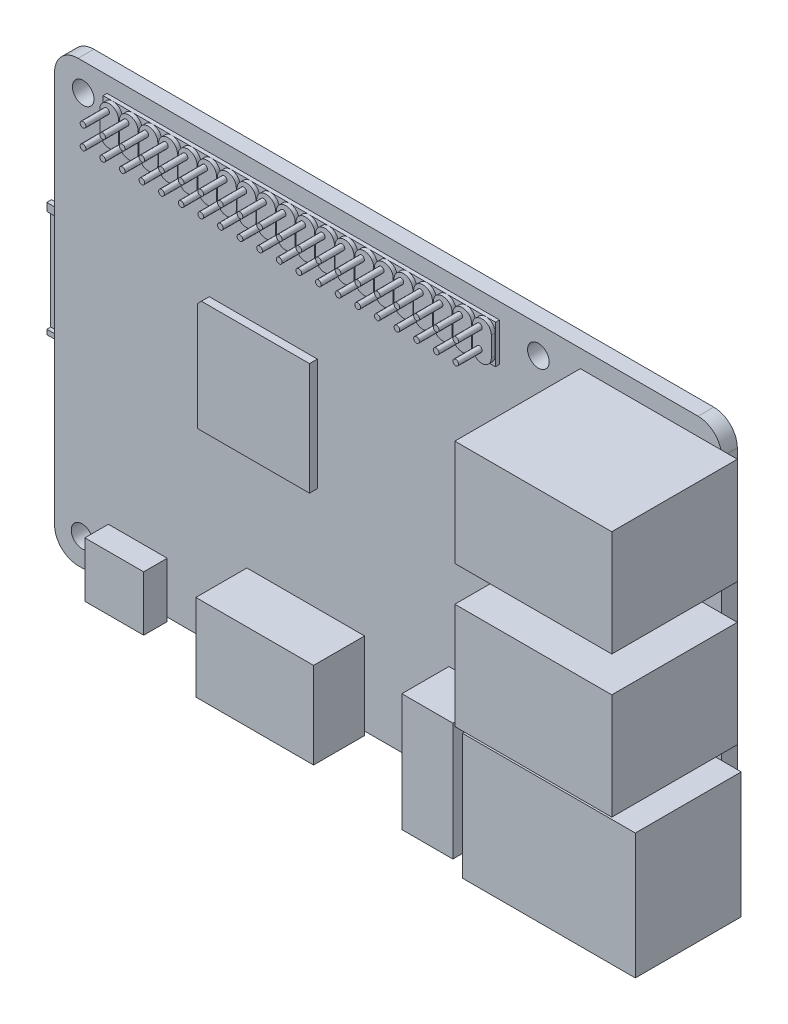
SolidWorks part; units mm, degrees
ref_plane "Plan de face" through (0, 0, 0) normal (0, 0, 1) x (1, 0, 0)
ref_plane "Plan de dessus" through (0, 0, 0) normal (0, 1, 0) x (1, 0, 0)
ref_plane "Plan de droite" through (0, 0, 0) normal (1, 0, 0) x (0, 0, -1)
sketch "Esquisse13" plane through (0, 0, 0) normal (0, 0, 1) x (1, 0, 0)
  line L1 (32.3051, 232.7529) -> (111.3051, 232.7529)
  line L2 (29.3051, 229.7529) -> (29.3051, 179.7529)
  line L3 (32.3051, 176.7529) -> (111.3051, 176.7529)
  line L4 (114.3051, 229.7529) -> (114.3051, 179.7529)
  arc A0 (114.3051, 229.7529) -> (111.3051, 232.7529) centre (111.3051, 229.7529) ccw
  arc A1 (114.3051, 179.7529) -> (111.3051, 176.7529) centre (111.3051, 179.7529) cw
  arc A2 (32.3051, 176.7529) -> (29.3051, 179.7529) centre (32.3051, 179.7529) cw
  arc A3 (32.3051, 232.7529) -> (29.3051, 229.7529) centre (32.3051, 229.7529) ccw
  dimension "D1" = 3
  dimension "D2" = 56
  dimension "D3" = 85
extrude "Boss.-Extru.6" add sketch "Esquisse13" along normal blind 2 separate body
sketch "Esquisse18" plane through (0, 0, 2) normal (0, 0, 1) x (1, 0, 0)
  line L0 (37.2566, 229.5258) -> (37.2566, 226.9968) construction
  line L1 (38.4539, 229.5258) -> (38.4539, 226.9968)
  line L2 (36.0594, 229.5258) -> (36.0594, 226.9968)
  line L3 (39.7566, 229.5258) -> (39.7566, 226.9968) construction
  line L4 (40.9539, 229.5258) -> (40.9539, 226.9968)
  line L5 (38.5594, 229.5258) -> (38.5594, 226.9968)
  line L6 (42.2566, 229.5258) -> (42.2566, 226.9968) construction
  line L7 (43.4539, 229.5258) -> (43.4539, 226.9968)
  line L8 (41.0594, 229.5258) -> (41.0594, 226.9968)
  line L9 (44.7566, 229.5258) -> (44.7566, 226.9968) construction
  line L10 (45.9539, 229.5258) -> (45.9539, 226.9968)
  line L11 (43.5594, 229.5258) -> (43.5594, 226.9968)
  line L12 (47.2566, 229.5258) -> (47.2566, 226.9968) construction
  line L13 (48.4539, 229.5258) -> (48.4539, 226.9968)
  line L14 (46.0594, 229.5258) -> (46.0594, 226.9968)
  line L15 (49.7566, 229.5258) -> (49.7566, 226.9968) construction
  line L16 (50.9539, 229.5258) -> (50.9539, 226.9968)
  line L17 (48.5594, 229.5258) -> (48.5594, 226.9968)
  line L18 (52.2566, 229.5258) -> (52.2566, 226.9968) construction
  line L19 (53.4539, 229.5258) -> (53.4539, 226.9968)
  line L20 (51.0594, 229.5258) -> (51.0594, 226.9968)
  line L21 (54.7566, 229.5258) -> (54.7566, 226.9968) construction
  line L22 (55.9539, 229.5258) -> (55.9539, 226.9968)
  line L23 (53.5594, 229.5258) -> (53.5594, 226.9968)
  line L24 (57.2566, 229.5258) -> (57.2566, 226.9968) construction
  line L25 (58.4539, 229.5258) -> (58.4539, 226.9968)
  line L26 (56.0594, 229.5258) -> (56.0594, 226.9968)
  line L27 (59.7566, 229.5258) -> (59.7566, 226.9968) construction
  line L28 (60.9539, 229.5258) -> (60.9539, 226.9968)
  line L29 (58.5594, 229.5258) -> (58.5594, 226.9968)
  line L30 (62.2566, 229.5258) -> (62.2566, 226.9968) construction
  line L31 (63.4539, 229.5258) -> (63.4539, 226.9968)
  line L32 (61.0594, 229.5258) -> (61.0594, 226.9968)
  line L33 (64.7566, 229.5258) -> (64.7566, 226.9968) construction
  line L34 (65.9539, 229.5258) -> (65.9539, 226.9968)
  line L35 (63.5594, 229.5258) -> (63.5594, 226.9968)
  line L36 (67.2566, 229.5258) -> (67.2566, 226.9968) construction
  line L37 (68.4539, 229.5258) -> (68.4539, 226.9968)
  line L38 (66.0594, 229.5258) -> (66.0594, 226.9968)
  line L39 (69.7566, 229.5258) -> (69.7566, 226.9968) construction
  line L40 (70.9539, 229.5258) -> (70.9539, 226.9968)
  line L41 (68.5594, 229.5258) -> (68.5594, 226.9968)
  line L42 (72.2566, 229.5258) -> (72.2566, 226.9968) construction
  line L43 (73.4539, 229.5258) -> (73.4539, 226.9968)
  line L44 (71.0594, 229.5258) -> (71.0594, 226.9968)
  line L45 (74.7566, 229.5258) -> (74.7566, 226.9968) construction
  line L46 (75.9539, 229.5258) -> (75.9539, 226.9968)
  line L47 (73.5594, 229.5258) -> (73.5594, 226.9968)
  line L48 (77.2566, 229.5258) -> (77.2566, 226.9968) construction
  line L49 (78.4539, 229.5258) -> (78.4539, 226.9968)
  line L50 (76.0594, 229.5258) -> (76.0594, 226.9968)
  line L51 (79.7566, 229.5258) -> (79.7566, 226.9968) construction
  line L52 (80.9539, 229.5258) -> (80.9539, 226.9968)
  line L53 (78.5594, 229.5258) -> (78.5594, 226.9968)
  line L54 (82.2566, 229.5258) -> (82.2566, 226.9968) construction
  line L55 (83.4539, 229.5258) -> (83.4539, 226.9968)
  line L56 (81.0594, 229.5258) -> (81.0594, 226.9968)
  line L57 (84.7566, 229.5258) -> (84.7566, 226.9968) construction
  line L58 (85.9539, 229.5258) -> (85.9539, 226.9968)
  line L59 (83.5594, 229.5258) -> (83.5594, 226.9968)
  arc A0 (38.4539, 229.5258) -> (36.0594, 229.5258) centre (37.2566, 229.5258) ccw
  arc A1 (36.0594, 226.9968) -> (38.4539, 226.9968) centre (37.2566, 226.9968) ccw
  arc A2 (40.9539, 229.5258) -> (38.5594, 229.5258) centre (39.7566, 229.5258) ccw
  arc A3 (38.5594, 226.9968) -> (40.9539, 226.9968) centre (39.7566, 226.9968) ccw
  arc A4 (43.4539, 229.5258) -> (41.0594, 229.5258) centre (42.2566, 229.5258) ccw
  arc A5 (41.0594, 226.9968) -> (43.4539, 226.9968) centre (42.2566, 226.9968) ccw
  arc A6 (45.9539, 229.5258) -> (43.5594, 229.5258) centre (44.7566, 229.5258) ccw
  arc A7 (43.5594, 226.9968) -> (45.9539, 226.9968) centre (44.7566, 226.9968) ccw
  arc A8 (48.4539, 229.5258) -> (46.0594, 229.5258) centre (47.2566, 229.5258) ccw
  arc A9 (46.0594, 226.9968) -> (48.4539, 226.9968) centre (47.2566, 226.9968) ccw
  arc A10 (50.9539, 229.5258) -> (48.5594, 229.5258) centre (49.7566, 229.5258) ccw
  arc A11 (48.5594, 226.9968) -> (50.9539, 226.9968) centre (49.7566, 226.9968) ccw
  arc A12 (53.4539, 229.5258) -> (51.0594, 229.5258) centre (52.2566, 229.5258) ccw
  arc A13 (51.0594, 226.9968) -> (53.4539, 226.9968) centre (52.2566, 226.9968) ccw
  arc A14 (55.9539, 229.5258) -> (53.5594, 229.5258) centre (54.7566, 229.5258) ccw
  arc A15 (53.5594, 226.9968) -> (55.9539, 226.9968) centre (54.7566, 226.9968) ccw
  arc A16 (58.4539, 229.5258) -> (56.0594, 229.5258) centre (57.2566, 229.5258) ccw
  arc A17 (56.0594, 226.9968) -> (58.4539, 226.9968) centre (57.2566, 226.9968) ccw
  arc A18 (60.9539, 229.5258) -> (58.5594, 229.5258) centre (59.7566, 229.5258) ccw
  arc A19 (58.5594, 226.9968) -> (60.9539, 226.9968) centre (59.7566, 226.9968) ccw
  arc A20 (63.4539, 229.5258) -> (61.0594, 229.5258) centre (62.2566, 229.5258) ccw
  arc A21 (61.0594, 226.9968) -> (63.4539, 226.9968) centre (62.2566, 226.9968) ccw
  arc A22 (65.9539, 229.5258) -> (63.5594, 229.5258) centre (64.7566, 229.5258) ccw
  arc A23 (63.5594, 226.9968) -> (65.9539, 226.9968) centre (64.7566, 226.9968) ccw
  arc A24 (68.4539, 229.5258) -> (66.0594, 229.5258) centre (67.2566, 229.5258) ccw
  arc A25 (66.0594, 226.9968) -> (68.4539, 226.9968) centre (67.2566, 226.9968) ccw
  arc A26 (70.9539, 229.5258) -> (68.5594, 229.5258) centre (69.7566, 229.5258) ccw
  arc A27 (68.5594, 226.9968) -> (70.9539, 226.9968) centre (69.7566, 226.9968) ccw
  arc A28 (73.4539, 229.5258) -> (71.0594, 229.5258) centre (72.2566, 229.5258) ccw
  arc A29 (71.0594, 226.9968) -> (73.4539, 226.9968) centre (72.2566, 226.9968) ccw
  arc A30 (75.9539, 229.5258) -> (73.5594, 229.5258) centre (74.7566, 229.5258) ccw
  arc A31 (73.5594, 226.9968) -> (75.9539, 226.9968) centre (74.7566, 226.9968) ccw
  arc A32 (78.4539, 229.5258) -> (76.0594, 229.5258) centre (77.2566, 229.5258) ccw
  arc A33 (76.0594, 226.9968) -> (78.4539, 226.9968) centre (77.2566, 226.9968) ccw
  arc A34 (80.9539, 229.5258) -> (78.5594, 229.5258) centre (79.7566, 229.5258) ccw
  arc A35 (78.5594, 226.9968) -> (80.9539, 226.9968) centre (79.7566, 226.9968) ccw
  arc A36 (83.4539, 229.5258) -> (81.0594, 229.5258) centre (82.2566, 229.5258) ccw
  arc A37 (81.0594, 226.9968) -> (83.4539, 226.9968) centre (82.2566, 226.9968) ccw
  arc A38 (85.9539, 229.5258) -> (83.5594, 229.5258) centre (84.7566, 229.5258) ccw
  arc A39 (83.5594, 226.9968) -> (85.9539, 226.9968) centre (84.7566, 226.9968) ccw
  point P2 (37.2566, 228.2613)
  point P11 (39.7566, 228.2613)
  point P18 (42.2566, 228.2613)
  point P25 (44.7566, 228.2613)
  point P32 (47.2566, 228.2613)
  point P39 (49.7566, 228.2613)
  point P46 (52.2566, 228.2613)
  point P53 (54.7566, 228.2613)
  point P60 (57.2566, 228.2613)
  point P67 (59.7566, 228.2613)
  point P74 (62.2566, 228.2613)
  point P81 (64.7566, 228.2613)
  point P88 (67.2566, 228.2613)
  point P95 (69.7566, 228.2613)
  point P102 (72.2566, 228.2613)
  point P109 (74.7566, 228.2613)
  point P116 (77.2566, 228.2613)
  point P123 (79.7566, 228.2613)
  point P130 (82.2566, 228.2613)
  point P137 (84.7566, 228.2613)
  dimension "D1" = 20
extrude "Boss.-Extru.8" add sketch "Esquisse18" along normal blind 1
sketch "Esquisse19" plane through (0, 0, 2) normal (0, 0, 1) x (1, 0, 0)
  line L1 (35.9943, 230.7231) -> (85.9948, 230.7231)
  line L2 (35.9943, 230.7231) -> (35.9943, 225.7996)
  line L3 (35.9943, 225.7996) -> (85.9948, 225.7996)
  line L4 (85.9948, 230.7231) -> (85.9948, 225.7996)
  arc A0 (36.0594, 226.9968) -> (38.4539, 226.9968) centre (37.2566, 226.9968) ccw construction
  arc A1 (38.4539, 229.5258) -> (36.0594, 229.5258) centre (37.2566, 229.5258) ccw construction
extrude "Boss.-Extru.9" add sketch "Esquisse19" along normal blind 0.5
sketch "Esquisse20" plane through (0, 0, 3) normal (0, 0, 1) x (1, 0, 0)
  line L0 (36.9236, 229.735) -> (36.9236, 227.2302) construction
  circle A0 centre (36.9236, 229.735) radius 0.3614
  circle A1 centre (36.9236, 227.2302) radius 0.3614
  circle A2 centre (39.4236, 229.735) radius 0.3614
  circle A3 centre (39.4236, 227.2302) radius 0.3614
  circle A4 centre (41.9236, 229.735) radius 0.3614
  circle A5 centre (41.9236, 227.2302) radius 0.3614
  circle A6 centre (44.4236, 229.735) radius 0.3614
  circle A7 centre (44.4236, 227.2302) radius 0.3614
  circle A8 centre (46.9236, 229.735) radius 0.3614
  circle A9 centre (46.9236, 227.2302) radius 0.3614
  circle A10 centre (49.4236, 229.735) radius 0.3614
  circle A11 centre (49.4236, 227.2302) radius 0.3614
  circle A12 centre (51.9236, 229.735) radius 0.3614
  circle A13 centre (51.9236, 227.2302) radius 0.3614
  circle A14 centre (54.4236, 229.735) radius 0.3614
  circle A15 centre (54.4236, 227.2302) radius 0.3614
  circle A16 centre (56.9236, 229.735) radius 0.3614
  circle A17 centre (56.9236, 227.2302) radius 0.3614
  circle A18 centre (59.4236, 229.735) radius 0.3614
  circle A19 centre (59.4236, 227.2302) radius 0.3614
  circle A20 centre (61.9236, 229.735) radius 0.3614
  circle A21 centre (61.9236, 227.2302) radius 0.3614
  circle A22 centre (64.4236, 229.735) radius 0.3614
  circle A23 centre (64.4236, 227.2302) radius 0.3614
  circle A24 centre (66.9236, 229.735) radius 0.3614
  circle A25 centre (66.9236, 227.2302) radius 0.3614
  circle A26 centre (69.4236, 229.735) radius 0.3614
  circle A27 centre (69.4236, 227.2302) radius 0.3614
  circle A28 centre (71.9236, 229.735) radius 0.3614
  circle A29 centre (71.9236, 227.2302) radius 0.3614
  circle A30 centre (74.4236, 229.735) radius 0.3614
  circle A31 centre (74.4236, 227.2302) radius 0.3614
  circle A32 centre (76.9236, 229.735) radius 0.3614
  circle A33 centre (76.9236, 227.2302) radius 0.3614
  circle A34 centre (79.4236, 229.735) radius 0.3614
  circle A35 centre (79.4236, 227.2302) radius 0.3614
  circle A36 centre (81.9236, 229.735) radius 0.3614
  circle A37 centre (81.9236, 227.2302) radius 0.3614
  circle A38 centre (84.4236, 229.735) radius 0.3614
  circle A39 centre (84.4236, 227.2302) radius 0.3614
  dimension "D1" = 20
extrude "Boss.-Extru.10" add sketch "Esquisse20" along normal blind 3
sketch "Esquisse21" plane through (0, 0, 2) normal (0, 0, 1) x (1, 0, 0)
  line L0 (48.4885, 214.2688) -> (49.0165, 214.7968)
  line L1 (62.7885, 200.4968) -> (48.4885, 200.4968)
  line L2 (62.7885, 200.4968) -> (62.7885, 214.7968)
  line L3 (62.7885, 214.7968) -> (49.0165, 214.7968)
  line L4 (48.4885, 200.4968) -> (48.4885, 214.2688)
  line L5 (91.8038, 213.7838) -> (92.0748, 213.5724)
  line L6 (83.9048, 205.5938) -> (92.0748, 205.5938)
  line L7 (83.9048, 205.5938) -> (83.9048, 213.7838)
  line L8 (83.9048, 213.7838) -> (91.8038, 213.7838)
  line L9 (92.0748, 205.5938) -> (92.0748, 213.5724)
  dimension "D1" = 14.3
  dimension "D2" = 14.3
  dimension "D3" = 8.17
  dimension "D4" = 8.19
extrude "Boss.-Extru.11" add sketch "Esquisse21" along normal blind 1
sketch "Esquisse22" plane through (0, 0, 0) normal (0, 0, -1) x (-1, 0, 0)
  line L0 (-77.9075, 215.1199) -> (-77.5535, 215.4739)
  line L1 (-65.8326, 203.3272) -> (-77.9075, 203.3272)
  line L2 (-65.8326, 203.3272) -> (-65.8326, 215.4739)
  line L3 (-65.8326, 215.4739) -> (-77.5535, 215.4739)
  line L4 (-77.9075, 203.3272) -> (-77.9075, 215.1199)
extrude "Boss.-Extru.12" add sketch "Esquisse22" along normal blind 1
sketch "Esquisse23" plane through (0, 0, 2) normal (0, 0, 1) x (1, 0, 0)
  line L0 (32.3051, 176.7529) -> (111.3051, 176.7529) construction
  line L1 (29.3051, 229.7529) -> (29.3051, 179.7529) construction
  circle A0 centre (32.9513, 229.2529) radius 1.375
  circle A1 centre (32.8051, 180.2529) radius 1.375
  circle A2 centre (90.8051, 180.2529) radius 1.375
  circle A3 centre (90.9513, 229.2529) radius 1.375
  point P12 (0, 0)
  point P13 (0, 0)
  point P14 (0, 0)
  dimension "D7" = 2.75
  dimension "D1" = 58
  dimension "D2" = 58
  dimension "D3" = 49
  dimension "D4" = 49
  dimension "D5" = 3.5
  dimension "D6" = 3.5
extrude "Enlèv. mat.-Extru.1" cut sketch "Esquisse23" against normal blind 21
sketch "Esquisse24" plane through (0, 0, 0) normal (0, 0, -1) x (-1, 0, 0)
  line L0 (-111.3051, 232.7529) -> (-32.3051, 232.7529) construction
  line L1 (-43.9051, 212.8529) -> (-26.3051, 212.8529)
  line L2 (-43.9051, 212.8529) -> (-43.9051, 198.2529)
  line L3 (-43.9051, 198.2529) -> (-26.3051, 198.2529)
  line L4 (-26.3051, 212.8529) -> (-26.3051, 198.2529)
  line L5 (-29.3051, 229.7529) -> (-29.3051, 179.7529) construction
  dimension "D1" = 19.9
  dimension "D2" = 17.6
  dimension "D3" = 3
  dimension "D4" = 14.6
extrude "Boss.-Extru.13" add sketch "Esquisse24" along normal blind 0.6
sketch "Esquisse25" plane through (26.3051, 0, 0) normal (-1, 0, 0) x (0, 0, 1)
  line L0 (-0.6, 212.8529) -> (0, 212.8529) construction
  line L1 (-0.5, 211.8529) -> (0, 211.8529)
  line L2 (-0.5, 211.8529) -> (-0.5, 198.8529)
  line L3 (-0.5, 198.8529) -> (0, 198.8529)
  line L4 (0, 211.8529) -> (0, 198.8529)
  line L5 (0, 229.7529) -> (0, 212.8529) construction
  line L6 (0, 198.2529) -> (0, 212.8529) construction
  line L7 (0, 203.3272) -> (0, 215.4739) construction
  dimension "D1" = 0.5
  dimension "D2" = 13
  dimension "D3" = 1
extrude "Enlèv. mat.-Extru.2" cut sketch "Esquisse25" against normal blind 11
sketch "Sketch1" plane through (0, 0, 2) normal (0, 0, 1) x (1, 0, 0)
  line L0 (32.3051, 176.7529) -> (111.3051, 176.7529) construction
  line L1 (36.1551, 176.2529) -> (43.6551, 176.2529)
  line L2 (36.1551, 176.2529) -> (36.1551, 183.2529)
  line L3 (36.1551, 183.2529) -> (43.6551, 183.2529)
  line L4 (43.6551, 176.2529) -> (43.6551, 183.2529)
  line L5 (39.9051, 183.2529) -> (39.9051, 176.2529) construction
  line L6 (29.3051, 229.7529) -> (29.3051, 179.7529) construction
  dimension "D1" = 7.5
  dimension "D2" = 7
  dimension "D3" = 0.5
  dimension "D4" = 10.6
extrude "Boss-Extrude1" add sketch "Sketch1" along normal blind 3
sketch "Sketch2" plane through (0, 0, 2) normal (0, 0, 1) x (1, 0, 0)
  line L0 (114.3051, 179.7529) -> (114.3051, 229.7529) construction
  line L1 (94.8051, 180.2529) -> (116.8051, 180.2529)
  line L2 (94.8051, 180.2529) -> (94.8051, 196.2529)
  line L3 (94.8051, 196.2529) -> (116.8051, 196.2529)
  line L4 (116.8051, 180.2529) -> (116.8051, 196.2529)
  line L5 (94.8051, 188.2529) -> (116.8051, 188.2529) construction
  line L6 (43.6551, 176.7529) -> (111.3051, 176.7529) construction
  dimension "D1" = 16
  dimension "D2" = 2.5
  dimension "D3" = 11.5
  dimension "D4" = 22
extrude "Boss-Extrude2" add sketch "Sketch2" along normal blind 13.5
sketch "Sketch3" plane through (0, 0, 2) normal (0, 0, 1) x (1, 0, 0)
  line L0 (61.3051, 187.2529) -> (61.3051, 176.2529) construction
  line L1 (53.8051, 187.2529) -> (68.8051, 187.2529)
  line L2 (53.8051, 187.2529) -> (53.8051, 176.2529)
  line L3 (53.8051, 176.2529) -> (68.8051, 176.2529)
  line L4 (68.8051, 187.2529) -> (68.8051, 176.2529)
  line L5 (43.6551, 176.7529) -> (111.3051, 176.7529) construction
  line L6 (29.3051, 229.7529) -> (29.3051, 179.7529) construction
  dimension "D1" = 15
  dimension "D2" = 11
  dimension "D3" = 0.5
  dimension "D4" = 32
extrude "Boss-Extrude3" add sketch "Sketch3" along normal blind 6.5
sketch "Sketch4" plane through (0, 0, 2) normal (0, 0, 1) x (1, 0, 0)
  line L0 (68.8051, 176.7529) -> (111.3051, 176.7529) construction
  line L1 (79.5551, 189.2529) -> (86.0551, 189.2529)
  line L2 (79.5551, 189.2529) -> (79.5551, 174.2529)
  line L3 (79.5551, 174.2529) -> (86.0551, 174.2529)
  line L4 (86.0551, 189.2529) -> (86.0551, 174.2529)
  line L5 (82.8051, 189.2529) -> (82.8051, 174.2529) construction
  line L6 (29.3051, 229.7529) -> (29.3051, 179.7529) construction
  dimension "D1" = 6.5
  dimension "D2" = 15
  dimension "D3" = 2.5
  dimension "D4" = 53.5
extrude "Boss-Extrude4" add sketch "Sketch4" along normal blind 6
sketch "Sketch5" plane through (0, 174.2529, 0) normal (0, -1, 0) x (1, 0, 0)
  circle A0 centre (82.8051, 5.1032) radius 1.75
  dimension "D1" = 3.5
extrude "Cut-Extrude1" cut sketch "Sketch5" against normal blind 12
sketch "Sketch6" plane through (0, 0, 2) normal (0, 0, 1) x (1, 0, 0)
  line L0 (114.3051, 196.2529) -> (114.3051, 229.7529) construction
  line L1 (96.3051, 199.0029) -> (116.3051, 199.0029)
  line L2 (96.3051, 199.0029) -> (96.3051, 212.5029)
  line L3 (96.3051, 212.5029) -> (116.3051, 212.5029)
  line L4 (116.3051, 199.0029) -> (116.3051, 212.5029)
  line L5 (96.3051, 205.7529) -> (116.3051, 205.7529) construction
  line L6 (86.0551, 176.7529) -> (111.3051, 176.7529) construction
  dimension "D1" = 13.5
  dimension "D2" = 2
  dimension "D3" = 20
  dimension "D4" = 29
extrude "Boss-Extrude5" add sketch "Sketch6" along normal blind 16
sketch "Sketch7" plane through (0, 0, 2) normal (0, 0, 1) x (1, 0, 0)
  line L0 (96.3051, 223.7529) -> (116.3051, 223.7529) construction
  line L1 (96.3051, 217.0029) -> (116.3051, 217.0029)
  line L2 (96.3051, 217.0029) -> (96.3051, 230.5029)
  line L3 (96.3051, 230.5029) -> (116.3051, 230.5029)
  line L4 (116.3051, 217.0029) -> (116.3051, 230.5029)
  line L5 (96.3051, 212.5029) -> (96.3051, 199.0029) construction
  line L6 (116.3051, 199.0029) -> (116.3051, 212.5029) construction
  line L7 (111.3051, 232.7529) -> (32.3051, 232.7529) construction
  line L8 (86.0551, 176.7529) -> (111.3051, 176.7529) construction
  dimension "D1" = 47
extrude "Boss-Extrude6" add sketch "Sketch7" along normal blind 16
